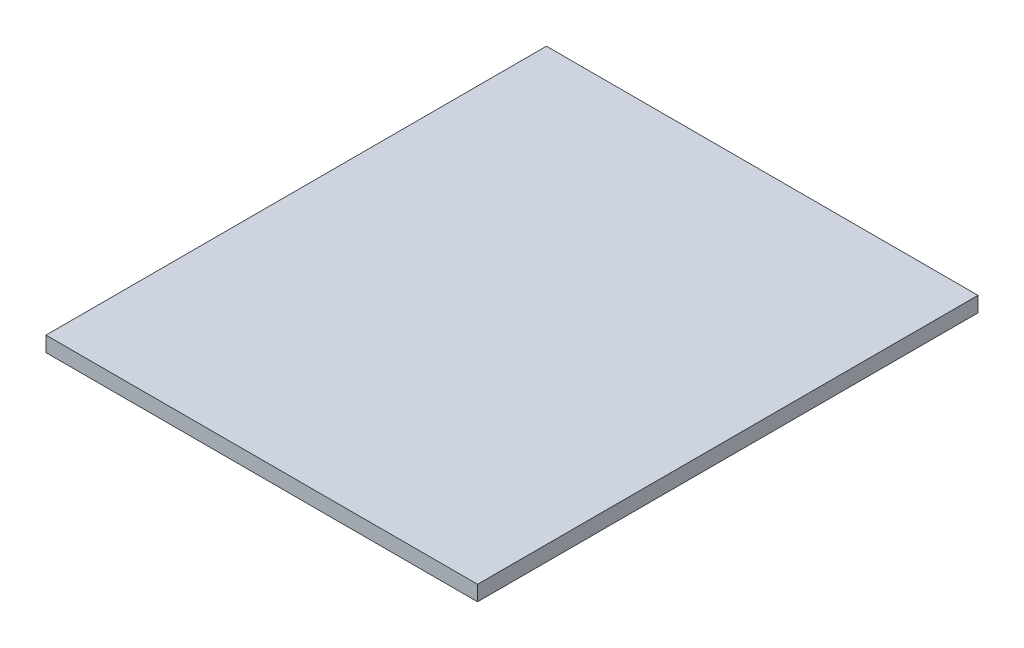
SolidWorks part; units mm, degrees
ref_plane "Front Plane" through (0, 0, 0) normal (0, 0, 1) x (1, 0, 0)
ref_plane "Top Plane" through (0, 0, 0) normal (0, 1, 0) x (1, 0, 0)
ref_plane "Right Plane" through (0, 0, 0) normal (1, 0, 0) x (0, 0, -1)
sketch "Sketch1" plane through (0, 0, 0) normal (0, 1, 0) x (1, 0, 0)
  line L1 (-44.2815, 20.698) -> (40.9185, 20.698)
  line L2 (-44.2815, 20.698) -> (-44.2815, -78.102)
  line L3 (-44.2815, -78.102) -> (40.9185, -78.102)
  line L4 (40.9185, 20.698) -> (40.9185, -78.102)
  dimension "D1" = 85.2
  dimension "D2" = 98.8
extrude "Boss-Extrude1" add sketch "Sketch1" along normal blind 3
equation "\"Fit\"= 1"
equation "\"cover width\"= 98.8"
equation "\"bottom 2 length\" = 85.2"
equation "\"thinner acrylic\"= 3"
equation "\"D1@Sketch1\"=\"bottom 2 length\""
equation "\"D2@Sketch1\"=\"cover width\""
equation "\"D1@Boss-Extrude1\"=\"thinner acrylic\""
